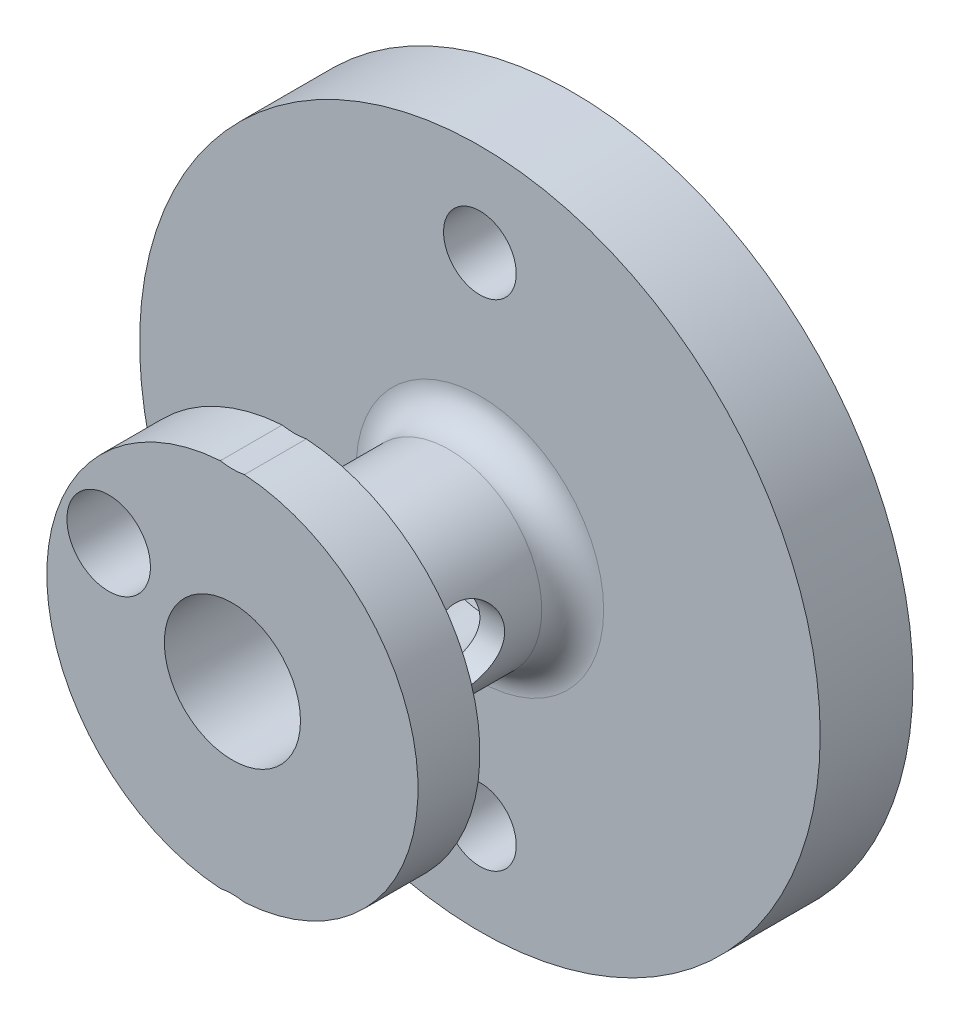
SolidWorks part; units mm, degrees
material "ABS"
ref_plane "Front Plane" through (0, 0, 0) normal (0, 0, 1) x (1, 0, 0)
ref_plane "Top Plane" through (0, 0, 0) normal (0, 1, 0) x (1, 0, 0)
ref_plane "Right Plane" through (0, 0, 0) normal (1, 0, 0) x (0, 0, -1)
sketch "Sketch1" plane through (0, 0, 0) normal (0, 0, 1) x (1, 0, 0)
  line L0 (0, 11) -> (0, -11) construction
  line L1 (0, 0) -> (-11, 0) construction
  circle A0 centre (0, 0) radius 11
  circle A1 centre (0, 0) radius 4.175
  point P24 (0, 0)
  dimension "D1" = 22
  dimension "D2" = 8.35
extrude "Main Body" add sketch "Sketch1" along normal mid plane 11
sketch "Sketch2" plane through (0, 0, 5.5) normal (0, 0, 1) x (1, 0, 0)
  circle A0 centre (0, 0) radius 4.175 construction
  circle A1 centre (0, 0) radius 4.175
  circle A2 centre (0, 0) radius 2.2
  dimension "D1" = 4.4
extrude "Main Bolt Surface" add sketch "Sketch2" against normal offset from surface (8.15 mm away) 2.85 up to face at (11, 0, -5.5)
ref_point "Ref Center"
sketch "Sketch7" plane through (0, 0, 5.5) normal (0, 0, 1) x (1, 0, 0)
  line L0 (0, 0) -> (0, 8) construction
  line L1 (0, 0) -> (0, -8) construction
  circle A1 centre (0, -8) radius 1.175
  circle A3 centre (0, 8) radius 1.175
  dimension "D2" = 8
  dimension "D3" = 2.35
  dimension "D4" = 2.35
  dimension "D1" = 16
extrude "Cut-Extrude4" cut sketch "Sketch7" against normal through all
sketch "Sketch8" plane through (0, 0, 5.5) normal (0, 0, 1) x (1, 0, 0)
  line L0 (0, 8) -> (0, 6.825) construction
  line L1 (0, 8) -> (0, 0) construction
  line L2 (0, -8) -> (0, 0) construction
  circle A0 centre (0, 8) radius 2.05
  circle A1 centre (0, -8) radius 2.05
  dimension "D1" = 4.1
extrude "Cut-Extrude5" cut sketch "Sketch8" against normal offset from surface (2 mm away) 2 up to face at (-1.175, -8, 5.5)
sketch "Sketch10" plane through (0, 0, 5.5) normal (0, 0, 1) x (1, 0, 0)
  circle A0 centre (0, 0) radius 6
  circle A1 centre (0, 0) radius 11
  dimension "D1" = 12
sketch "Sketch11" plane through (0, 0, 0) normal (0, 0, 1) x (1, 0, 0)
  circle A1 centre (0, 0) radius 11
  circle A2 centre (0, 0) radius 3
  circle A4 centre (0, 8) radius 2.05 construction
  dimension "D1" = 6
extrude "Cut-Extrude9" cut sketch "Sketch11" along normal blind 6 from offset 2.5 offset against normal yes
extrude "Cut-Extrude10" cut sketch "Sketch10" against normal up to next
fillet "Fillet2" radius 1 1 edges at (3, 0, -2.5)
sketch "Sketch12" plane through (0, 0, 0) normal (1, 0, 0) x (0, 0, -1)
  line L0 (-3.5, 0) -> (1.5, 0) construction
  line L1 (-3.5, -3) -> (-3.5, 3) construction
  line L2 (1.5, 3) -> (1.5, -3) construction
  line L3 (1.5, 0) -> (-1, 0) construction
  line L4 (-1, 0) -> (-1, 3) construction
  line L5 (1.5, 3) -> (-3.5, 3) construction
  circle A0 centre (-1, 0) radius 1.3
extrude "Cut-Extrude12" cut sketch "Sketch12" against normal through all both and the other way through all
sketch "Sketch13" plane through (0, 0, 5.5) normal (0, 0, 1) x (1, 0, 0)
  circle A0 centre (-3.9994, 1.877) radius 1.35
  point P2 (-3.821, 1.8485)
  point P3 (-3.9994, 1.877)
  dimension "D1" = 2.7
extrude "Cut-Extrude13" cut sketch "Sketch13" against normal blind 5.5
